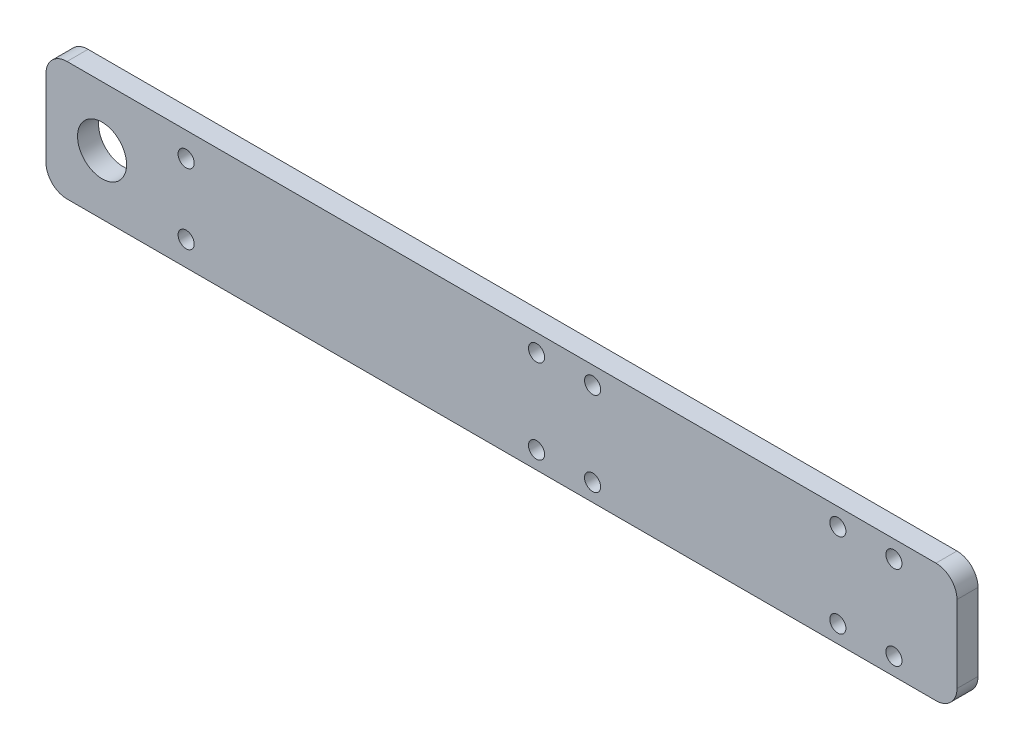
SolidWorks part; units mm, degrees
material "A-玻璃纤维"
ref_plane "前视基准面" through (0, 0, 0) normal (0, 0, 1) x (1, 0, 0)
ref_plane "上视基准面" through (0, 0, 0) normal (0, 1, 0) x (1, 0, 0)
ref_plane "右视基准面" through (0, 0, 0) normal (1, 0, 0) x (0, 0, -1)
sketch "草图1" plane through (0, 0, 0) normal (0, 0, 1) x (1, 0, 0)
  line L0 (0, 30.3555) -> (0, -35.5427) construction
  line L1 (-65, -8.5) -> (65, -8.5)
  line L2 (-65, -8.5) -> (-65, 8.5)
  line L3 (-65, 8.5) -> (65, 8.5)
  line L4 (65, -8.5) -> (65, 8.5)
  line L5 (-65, -8.5) -> (65, 8.5) construction
  line L6 (-65, 8.5) -> (65, -8.5) construction
  line L7 (79.7562, 0) -> (-74.892, 0) construction
  circle A0 centre (-57, 0) radius 3.5
  circle A1 centre (-45, 5) radius 1.15
  circle A2 centre (-45, -5) radius 1.15
  circle A3 centre (5, 6) radius 1.15
  circle A4 centre (13, 6) radius 1.15
  circle A5 centre (5, -6) radius 1.15
  circle A6 centre (13, -6) radius 1.15
  circle A7 centre (48, 6) radius 1.15
  circle A8 centre (56, 6) radius 1.15
  circle A9 centre (56, -6) radius 1.15
  circle A10 centre (48, -6) radius 1.15
  point P0 (0, 0)
  dimension "D3" = 10
  dimension "D4" = 2.3
  dimension "D5" = 7
  dimension "D6" = 8
  dimension "D7" = 12
  dimension "D8" = 2.3
  dimension "D9" = 8
  dimension "D10" = 12
  dimension "D11" = 50
  dimension "D12" = 8
  dimension "D13" = 35
  dimension "D1" = 130
  dimension "D2" = 17
extrude "凸台-拉伸1" add sketch "草图1" along normal blind 3
fillet "圆角1" radius 3 4 edges at (65, -8.5, 1.5) (65, 8.5, 1.5) (-65, -8.5, 1.5) (-65, 8.5, 1.5)
